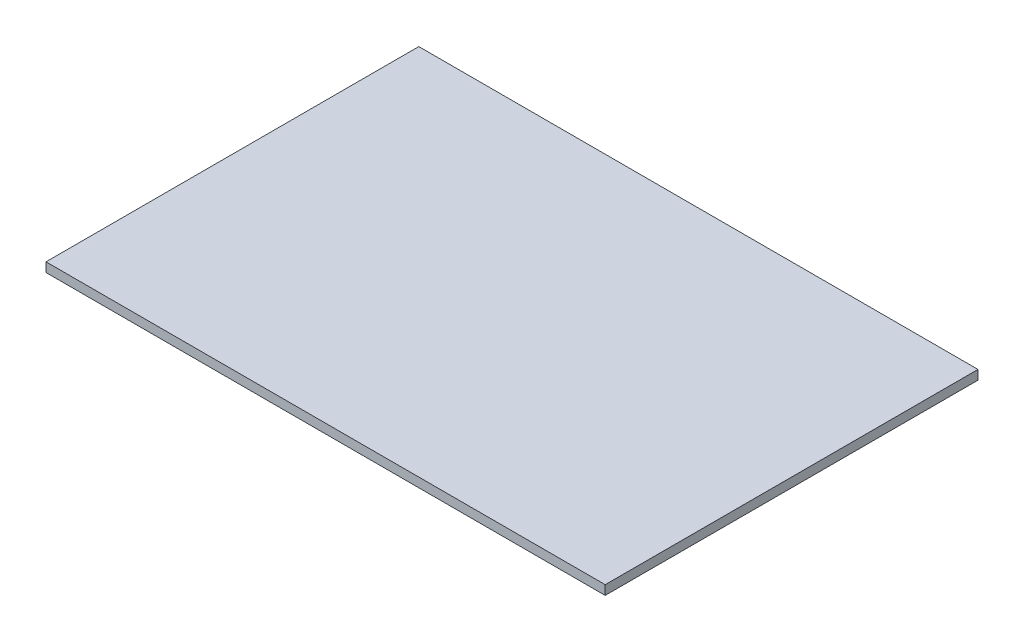
SolidWorks part; units mm, degrees
ref_plane "Front Plane" through (0, 0, 0) normal (0, 0, 1) x (1, 0, 0)
ref_plane "Top Plane" through (0, 0, 0) normal (0, 1, 0) x (1, 0, 0)
ref_plane "Right Plane" through (0, 0, 0) normal (1, 0, 0) x (0, 0, -1)
ref_plane "Plane1"
sketch "Sketch1" plane through (0, 0, 0) normal (0, 1, 0) x (-1, 0, 0)
  line L0 (8.2395, 4.7612) -> (-51.7605, 4.7612)
  line L1 (-51.7605, 4.7612) -> (-51.7605, -35.2388)
  line L2 (-51.7605, -35.2388) -> (8.2395, -35.2388)
  line L3 (8.2395, -35.2388) -> (8.2395, 4.7612)
  dimension "D1" = 60
  dimension "D2" = 40
extrude "Extrusion1" add sketch "Sketch1" along normal blind 1
